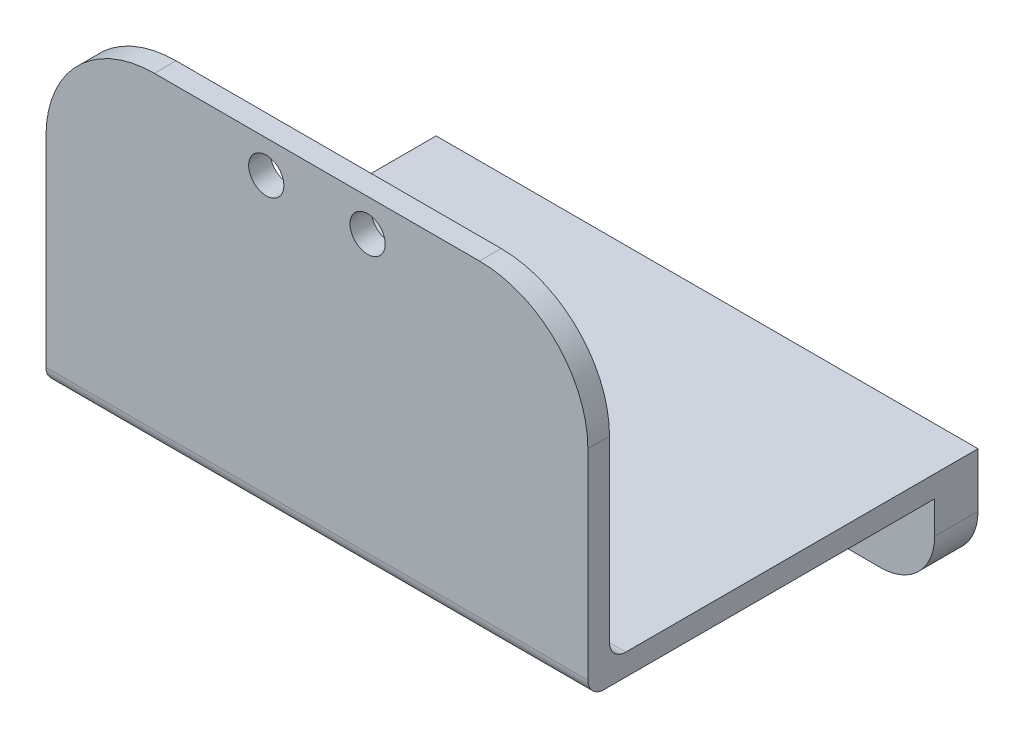
SolidWorks part; units mm, degrees
ref_plane "Front Plane" through (0, 0, 0) normal (0, 0, 1) x (1, 0, 0)
ref_plane "Top Plane" through (0, 0, 0) normal (0, 1, 0) x (1, 0, 0)
ref_plane "Right Plane" through (0, 0, 0) normal (1, 0, 0) x (0, 0, -1)
sketch "Sketch1" plane through (0, 0, 0) normal (0, 0, 1) x (1, 0, 0)
  line L0 (-29.0429, 19.0537) -> (-29.0429, 11.0537) construction
  line L1 (-54.0429, 19.0537) -> (-4.0429, 19.0537)
  line L2 (-54.0429, 19.0537) -> (-54.0429, 11.0537)
  line L3 (-54.0429, 11.0537) -> (-4.0429, 11.0537)
  line L4 (-4.0429, 19.0537) -> (-4.0429, 11.0537)
  line L5 (-41.1806, 19.0537) -> (-16.9053, 19.0537) construction
  line L6 (-54.0429, 15.0537) -> (-4.0429, 15.0537) construction
  circle A0 centre (-41.1806, 15.0537) radius 1.5
  circle A1 centre (-16.9053, 15.0537) radius 1.5
  dimension "D3" = 3
  dimension "D1" = 50
  dimension "D2" = 8
extrude "Boss-Extrude1" add sketch "Sketch1" along normal blind 4
sketch "Sketch2" plane through (0, 0, 4) normal (0, 0, 1) x (1, 0, 0)
  line L1 (-54.0429, 19.0537) -> (-4.0429, 19.0537)
  line L2 (-54.0429, 19.0537) -> (-54.0429, 21.0537)
  line L3 (-54.0429, 21.0537) -> (-4.0429, 21.0537)
  line L4 (-4.0429, 19.0537) -> (-4.0429, 21.0537)
  dimension "D1" = 2
extrude "Boss-Extrude2" add sketch "Sketch2" along normal blind 30 and the other way blind 4
sketch "Sketch3" plane through (-54.0429, 0, 0) normal (-1, 0, 0) x (0, 0, 1)
  line L1 (34, 19.0537) -> (36, 19.0537)
  line L2 (34, 19.0537) -> (34, 49.0537)
  line L3 (34, 49.0537) -> (36, 49.0537)
  line L4 (36, 19.0537) -> (36, 49.0537)
  dimension "D1" = 2
  dimension "D2" = 30
extrude "Boss-Extrude3" add sketch "Sketch3" against normal blind 50
sketch "Sketch4" plane through (0, 0, 36) normal (0, 0, 1) x (1, 0, 0)
  line L0 (-29.0429, 49.0537) -> (-29.0429, 19.0537) construction
  line L1 (-4.0429, 49.0537) -> (-54.0429, 49.0537) construction
  line L2 (-4.0429, 19.0537) -> (-54.0429, 19.0537) construction
  circle A0 centre (-24.3679, 46.0537) radius 1.625
  circle A1 centre (-33.7179, 46.0537) radius 1.625
  dimension "D1" = 3.25
  dimension "D2" = 4.675
  dimension "D3" = 3
fillet "Fillet1" radius 10 2 edges at (-4.0429, 49.0537, 35) (-54.0429, 49.0537, 35)
fillet "Fillet2" radius 5 2 edges at (-54.0429, 11.0537, 2) (-4.0429, 11.0537, 2)
fillet "Fillet3" radius 1.5 2 edges at (-29.0429, 19.0537, 36)
extrude "Cut-Extrude1" cut sketch "Sketch4" against normal blind 13
